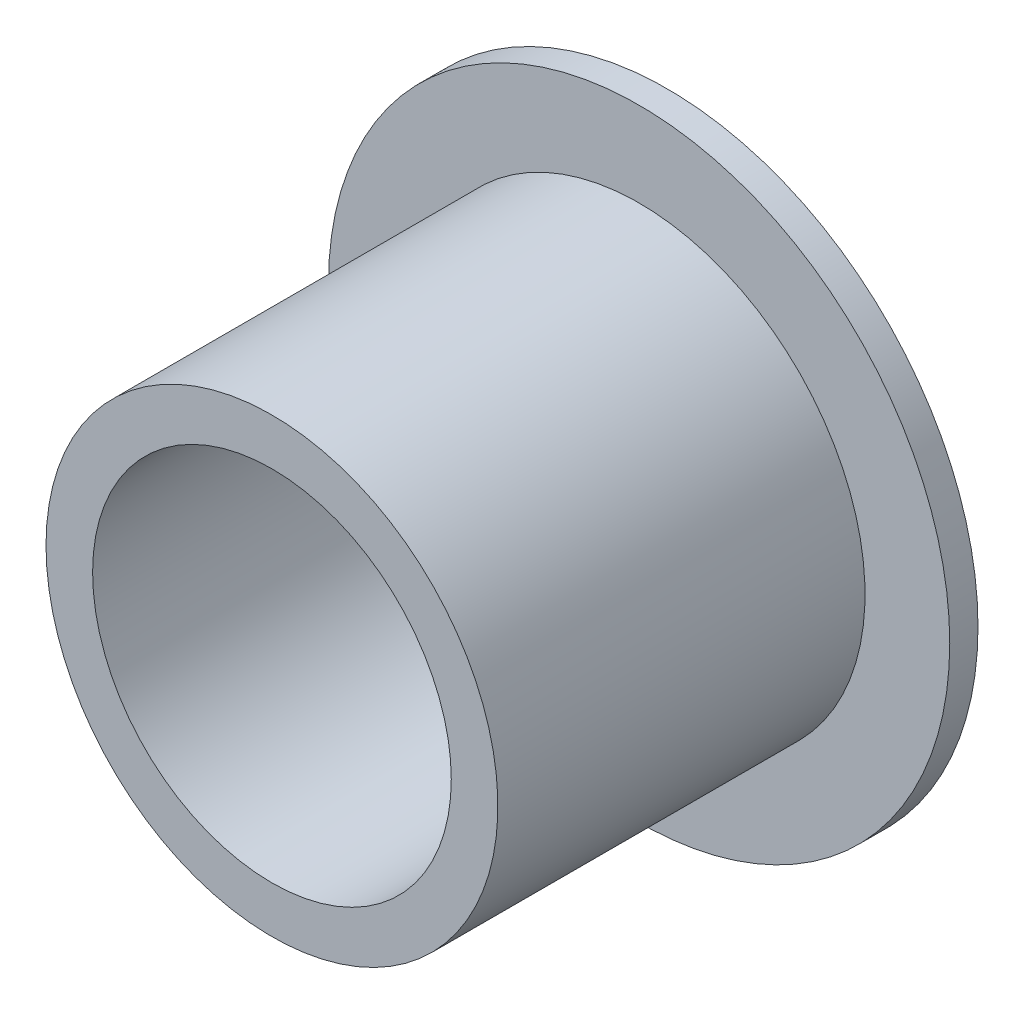
SolidWorks part; units mm, degrees
material "Brass"
ref_plane "Front Plane" through (0, 0, 0) normal (0, 0, 1) x (1, 0, 0)
ref_plane "Top Plane" through (0, 0, 0) normal (0, 1, 0) x (1, 0, 0)
ref_plane "Right Plane" through (0, 0, 0) normal (1, 0, 0) x (0, 0, -1)
sketch "Sketch1" plane through (0, 0, 0) normal (1, 0, 0) x (0, 0, -1)
  line L0 (0, 6.35) -> (0, 11)
  line L1 (0, 11) -> (-1, 11)
  line L2 (-1, 11) -> (-1, 8)
  line L3 (-1, 8) -> (-14, 8)
  line L4 (-14, 8) -> (-14, 6.35)
  line L5 (-14, 6.35) -> (0, 6.35)
  line L6 (0, 0) -> (-45.0043, 0) construction
  dimension "D1" = 1
  dimension "D2" = 12.7
  dimension "D3" = 16
  dimension "D4" = 3
  dimension "D5" = 14
revolve "Revolve1" add sketch "Sketch1" angle 360 about L6
